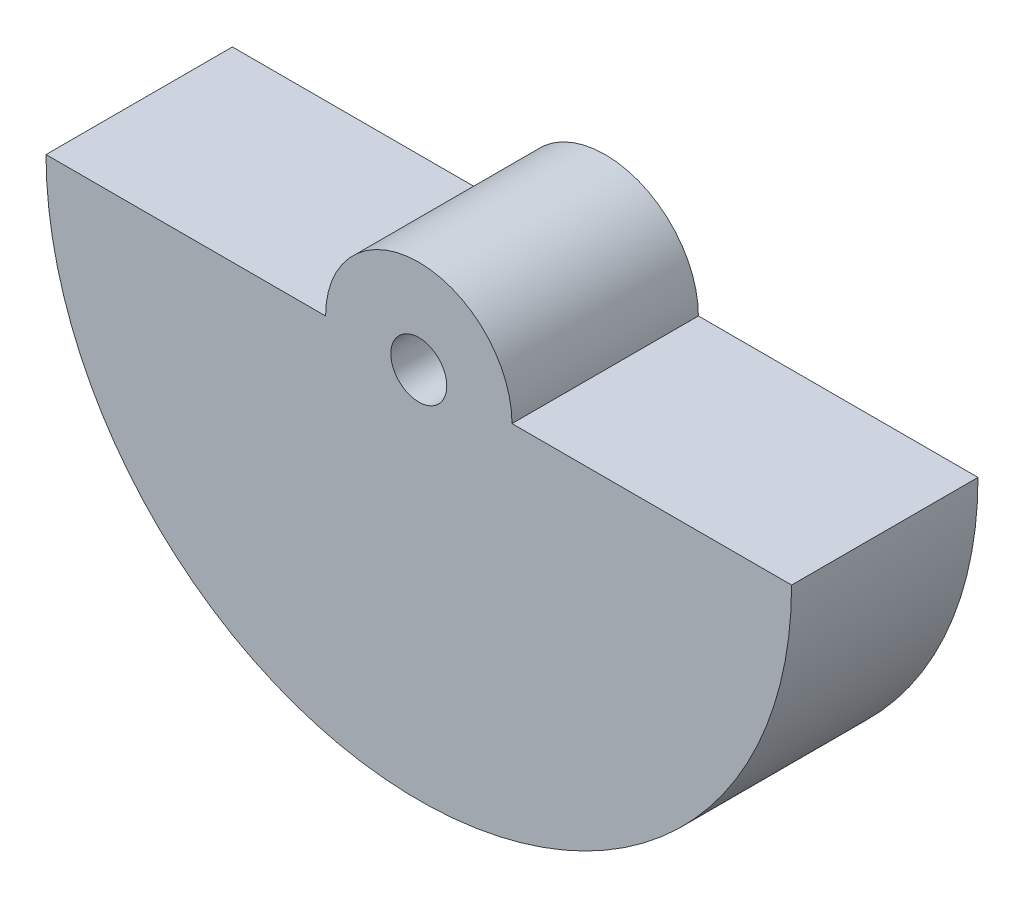
SolidWorks part; units mm, degrees
ref_plane "Front Plane" through (0, 0, 0) normal (0, 0, 1) x (1, 0, 0)
ref_plane "Top Plane" through (0, 0, 0) normal (0, 1, 0) x (1, 0, 0)
ref_plane "Right Plane" through (0, 0, 0) normal (1, 0, 0) x (0, 0, -1)
sketch "Sketch1" plane through (0, 0, 0) normal (0, 0, 1) x (1, 0, 0)
  line L0 (-3.4027, 21.5555) -> (76.5973, 21.5555)
  arc A0 (-3.4027, 21.5555) -> (76.5973, 21.5555) centre (36.5973, 21.5555) ccw
extrude "Boss-Extrude1" add sketch "Sketch1" along normal blind 20
sketch "Sketch2" plane through (0, 0, 0) normal (0, 0, -1) x (-1, 0, 0)
  line L0 (-76.5973, 21.5555) -> (3.4027, 21.5555) construction
  circle A0 centre (-36.5973, 21.5555) radius 10
extrude "Boss-Extrude2" add sketch "Sketch2" against normal up to surface (20 mm away) up to face at (36.5973, 1.5555, 20)
sketch "Sketch3" plane through (0, 0, 0) normal (0, 0, -1) x (-1, 0, 0)
  circle A0 centre (-36.5973, 21.5555) radius 3
  arc A1 (-26.5973, 21.5555) -> (-46.5973, 21.5555) centre (-36.5973, 21.5555) ccw construction
extrude "Cut-Extrude1" cut sketch "Sketch3" against normal up to surface (20 mm away) up to face at (36.5973, 14.0555, 20)
